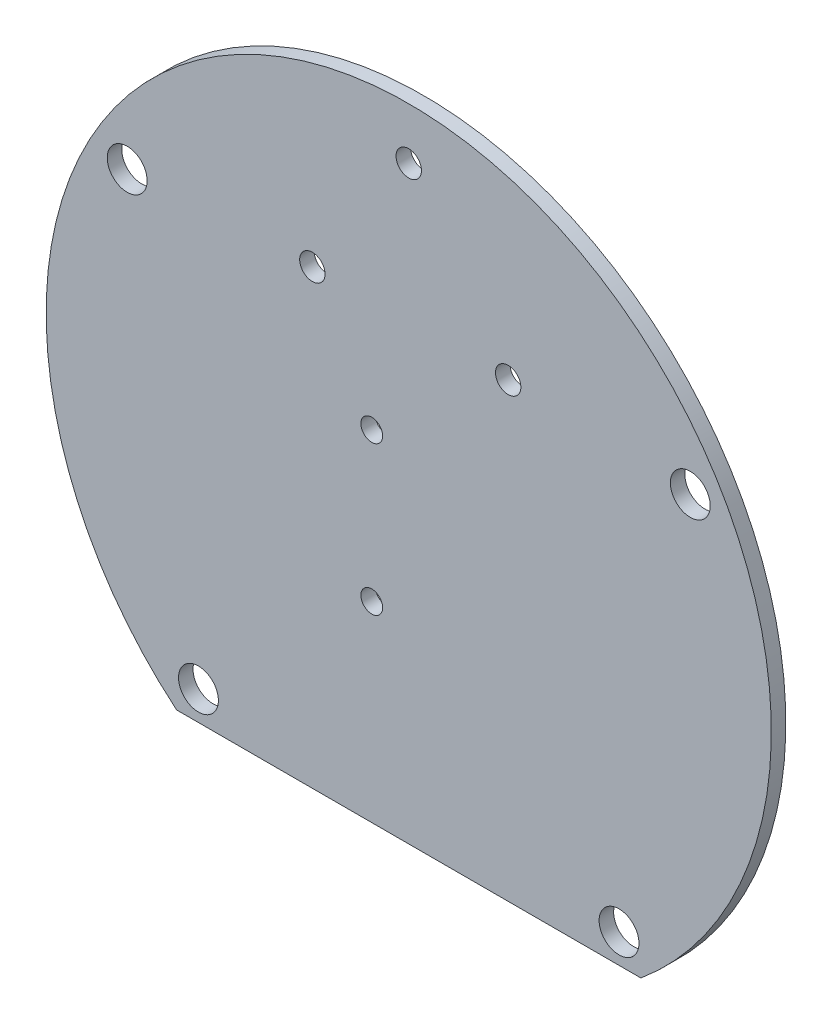
SolidWorks part; units mm, degrees
ref_plane "Plano frontal" through (0, 0, 0) normal (0, 0, 1) x (1, 0, 0)
ref_plane "Plano superior" through (0, 0, 0) normal (0, 1, 0) x (1, 0, 0)
ref_plane "Plano direito" through (0, 0, 0) normal (1, 0, 0) x (0, 0, -1)
sketch "Esboço1" plane through (0, 0, 0) normal (0, 0, 1) x (1, 0, 0)
  circle A0 centre (0, 0) radius 50
  dimension "D1" = 100
extrude "Ressalto-extrusão1" add sketch "Esboço1" along normal blind 2
sketch "Esboço2" plane through (0, 0, 2) normal (0, 0, 1) x (1, 0, 0)
  line L0 (0, 0) -> (0, 68.6386) construction
  line L1 (-61.9657, 0) -> (66.0984, 0) construction
  line L2 (-61.9657, -34.4093) -> (66.0984, -34.4093) construction
  circle A4 centre (-29, -34.4093) radius 2.75
  circle A5 centre (29, -34.4093) radius 2.75
  circle A6 centre (-38.8242, 22.7526) radius 2.75
  circle A7 centre (38.8242, 22.7526) radius 2.75
  point P9 (2.9328, -3.8481)
  dimension "D1" = 58
  dimension "D4" = 45
  dimension "D2" = 45
  dimension "D8" = 5.5
  dimension "D9" = 5.5
  dimension "D10" = 5.5
  dimension "D11" = 5.5
  dimension "D3" = 45
  dimension "D5" = 45
  dimension "D6" = 58
  dimension "D7" = 58
extrude "Corte-extrusão1" cut sketch "Esboço2" against normal blind 2
sketch "Esboço4" plane through (0, 0, 2) normal (0, 0, 1) x (1, 0, 0)
  line L0 (-40.7239, -38.4093) -> (44.5707, -38.4093)
  line L1 (-40.7239, -38.4093) -> (1.9234, -68.0022)
  line L2 (1.9234, -68.0022) -> (44.5707, -38.4093)
  circle A0 centre (-29, -34.4093) radius 2.75 construction
  dimension "D1" = 4
extrude "Corte-extrusão2" cut sketch "Esboço4" against normal blind 10 and the other way through all
sketch "Esboço5" plane through (0, 0, 0) normal (0, 0, -1) x (-1, 0, 0)
  line L0 (64.3082, 0) -> (-64.3082, 0) construction
  line L1 (0, 62.8144) -> (0, -62.8144) construction
  circle A1 centre (5.1, 8.5) radius 1.5
  circle A2 centre (5.1, -12) radius 1.5
  circle A3 centre (-13.71, 23.86) radius 1.75
  circle A4 centre (13.29, 23.86) radius 1.75
  circle A5 centre (0, 42.87) radius 1.75
  point P6 (0, 0)
  point P9 (0, 0)
  dimension "D1" = 5.1
  dimension "D5" = 23.86
  dimension "D2" = 5.1
  dimension "D3" = 12
  dimension "D4" = 8.5
  dimension "D6" = 13.71
  dimension "D7" = 13.29
  dimension "D8" = 23.86
  dimension "42,87" = 42.87
extrude "Corte-extrusão3" cut sketch "Esboço5" against normal blind 10
